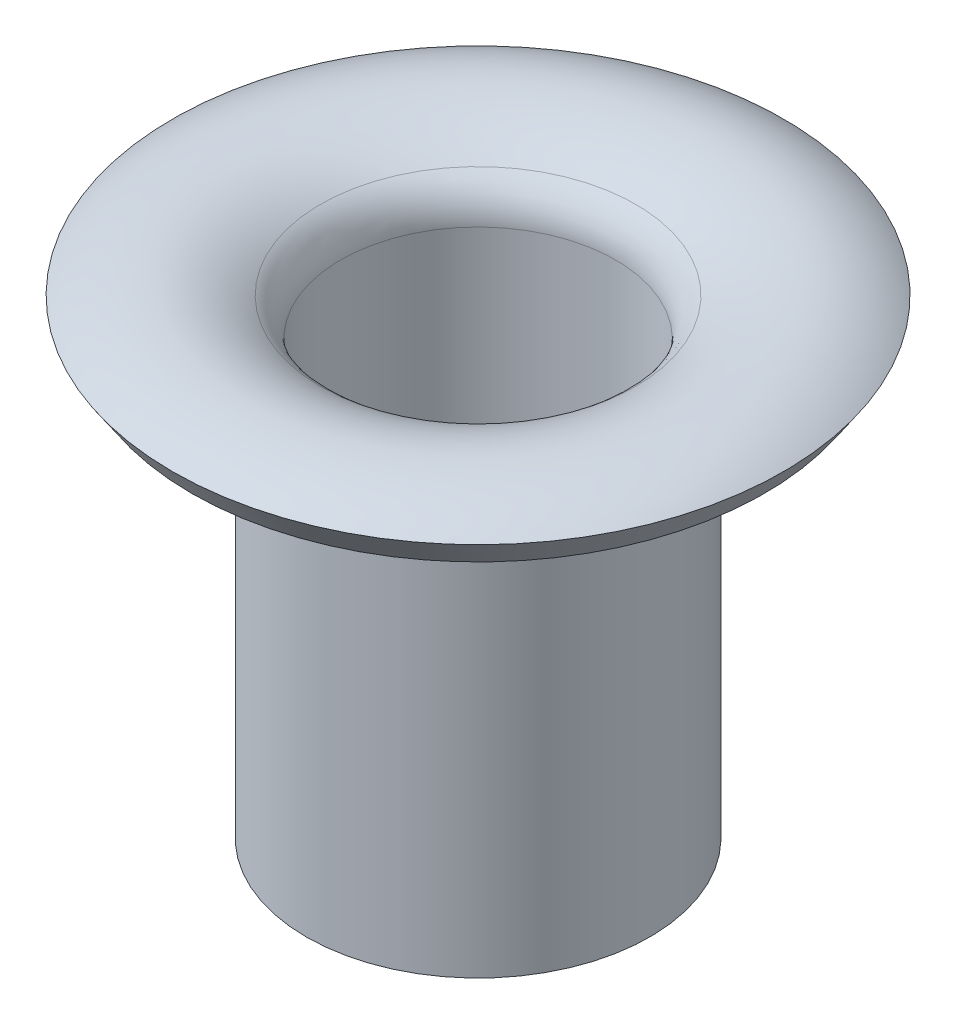
SolidWorks part; units mm, degrees
ref_plane "Plan de face" through (0, 0, 0) normal (0, 0, 1) x (1, 0, 0)
ref_plane "Plan de dessus" through (0, 0, 0) normal (0, 1, 0) x (1, 0, 0)
ref_plane "Plan de droite" through (0, 0, 0) normal (1, 0, 0) x (0, 0, -1)
sketch "Esquisse2" plane through (0, 0, 0) normal (0, 0, 1) x (1, 0, 0)
  line L0 (0, 0) -> (0, -5.4886) construction
  line L1 (1.5, -3.8541) -> (1.5, -0.0829)
  line L2 (2.0221, 0.1459) -> (2.0221, 0) construction
  arc A0 (1.5, -0.0829) -> (1.5441, 0) centre (1.6, -0.0829) cw
  arc A1 (1.5441, 0) -> (2.5, 0) centre (2.0221, -0.7098) cw
  dimension "D4" = 0.1
  dimension "D1" = 5
  dimension "D2" = 3
  dimension "D3" = 0.1459
  dimension "D5" = 4
revolve "Révol.-Mince1" add sketch "Esquisse2" angle 360 about L0 wall 0.3
